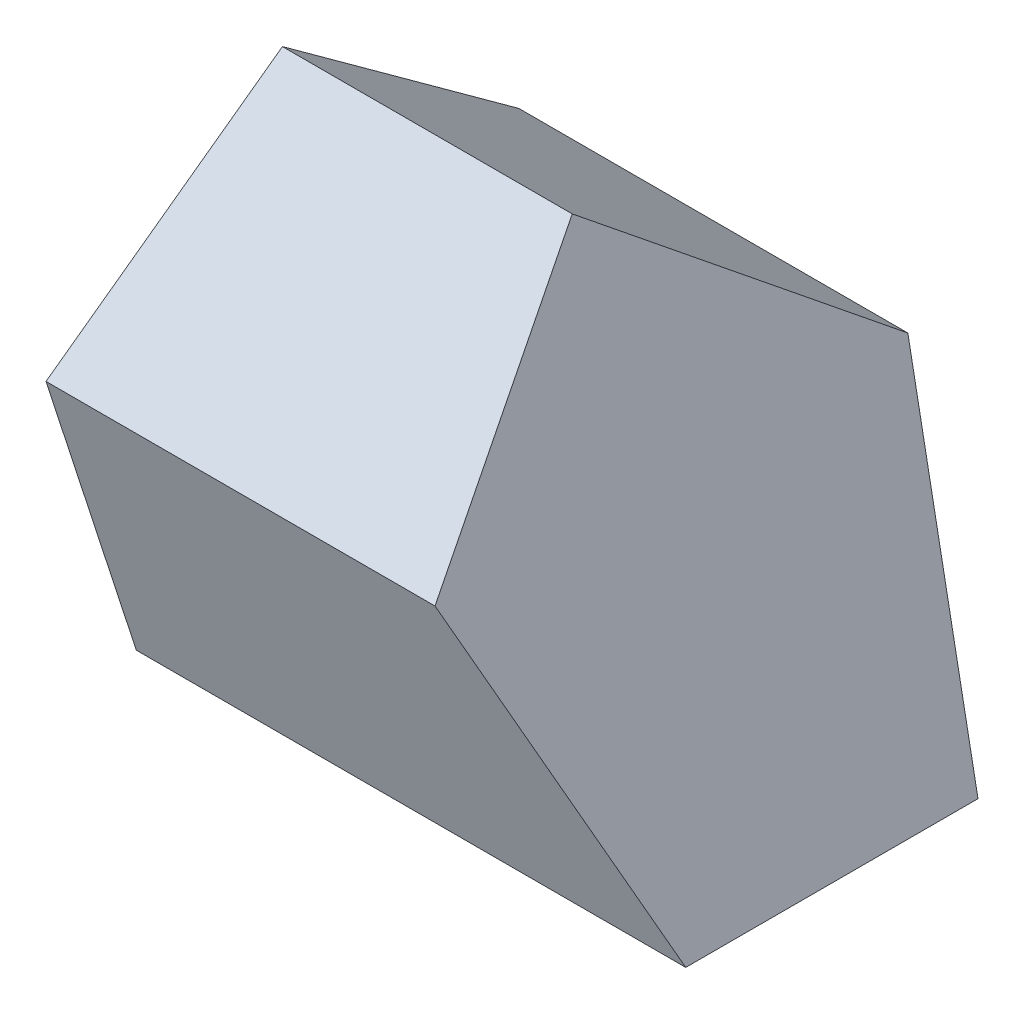
SolidWorks part; units mm, degrees
ref_plane "Front" through (0, 0, 0) normal (0, 0, 1) x (1, 0, 0)
ref_plane "Top" through (0, 0, 0) normal (0, 1, 0) x (1, 0, 0)
ref_plane "Right" through (0, 0, 0) normal (1, 0, 0) x (0, 0, -1)
sketch "Sketch1" plane through (0, 0, 0) normal (1, 0, 0) x (0, 0, -1)
  line L1 (18.1636, -25) -> (29.3893, 9.5492)
  line L2 (29.3893, 9.5492) -> (0, 30.9017)
  line L3 (0, 30.9017) -> (-29.3893, 9.5492)
  line L4 (-29.3893, 9.5492) -> (-18.1636, -25)
  line L5 (-18.1636, -25) -> (18.1636, -25)
  circle A0 centre (0, 0) radius 25 construction
extrude "Extrude1" add sketch "Sketch1" along normal blind 70
sketch "Sketch2" plane through (0, 0, 0) normal (0, 0, 1) x (1, 0, 0)
  line L4 (25, -25) -> (25, 25)
  arc A0 (25, -25) -> (25, 25) centre (25, 0) ccw
revolve "Revolve1" add sketch "Sketch2" angle 360 about L4
sketch "Sketch3" plane through (0, 0, 0) normal (0, 0, 1) x (1, 0, 0)
  line L0 (70, 30.9017) -> (36.0264, 30.9017)
  line L2 (36.0264, 30.9017) -> (68.3013, -25)
  line L5 (70, 30.9017) -> (70, -25)
  line L6 (70, -25) -> (68.3013, -25)
extrude "Cut-Extrude1" cut sketch "Sketch3" against normal mid plane 60
